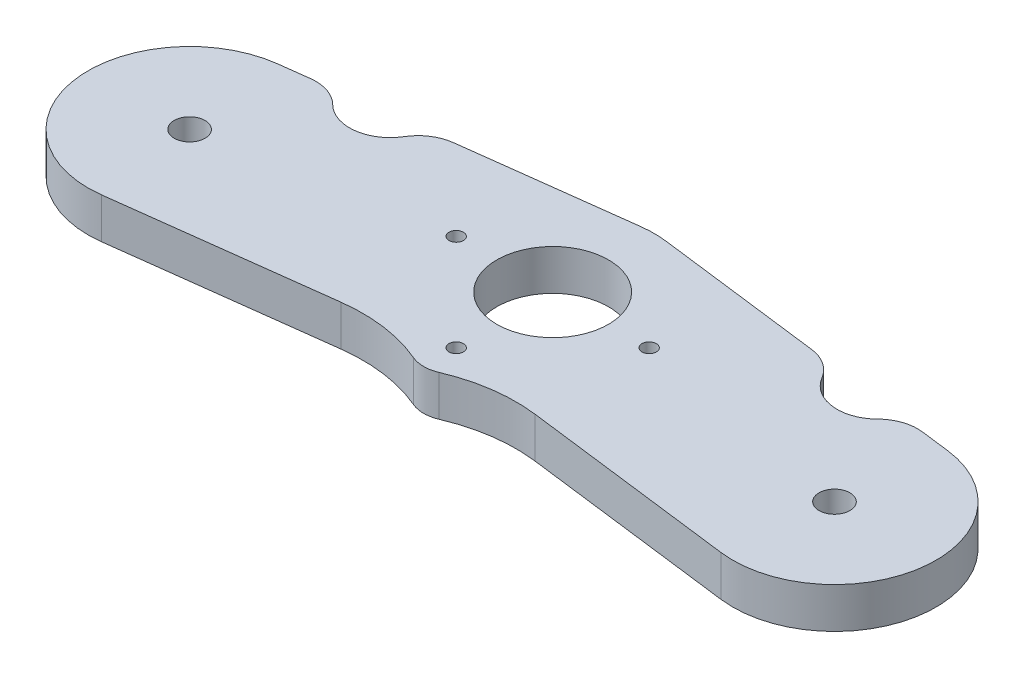
SolidWorks part; units mm, degrees
material "5052-H32"
ref_plane "Front Plane" through (0, 0, 0) normal (0, 0, 1) x (1, 0, 0)
ref_plane "Top Plane" through (0, 0, 0) normal (0, 1, 0) x (1, 0, 0)
ref_plane "Right Plane" through (0, 0, 0) normal (1, 0, 0) x (0, 0, -1)
sketch "Sketch1" plane through (0, 0, 0) normal (0, 1, 0) x (1, 0, 0)
  line L0 (50.8, 0) -> (-50.8, 0) construction
  line L1 (50.8, -15.875) -> (-50.8, -15.875) construction
  line L2 (50.8, 15.875) -> (-50.8, 15.875) construction
  line L3 (0, 0) -> (-50.4016, -6.35) construction
  line L6 (1.9844, -15.7505) -> (-48.4172, -22.1005)
  line L9 (-1.9844, 15.7505) -> (-52.3859, 9.4005)
  line L10 (0, 0) -> (50.4016, -6.35) construction
  line L11 (1.9844, 15.7505) -> (52.3859, 9.4005)
  line L12 (-1.9844, -15.7505) -> (48.4172, -22.1005)
  arc A0 (50.8, -15.875) -> (50.8, 15.875) centre (50.8, 0) ccw construction
  arc A1 (-50.8, 15.875) -> (-50.8, -15.875) centre (-50.8, 0) ccw construction
  arc A6 (1.9844, -15.7505) -> (-1.9844, 15.7505) centre (0, 0) ccw
  arc A7 (-52.3859, 9.4005) -> (-48.4172, -22.1005) centre (-50.4016, -6.35) ccw
  arc A8 (1.9844, 15.7505) -> (-1.9844, -15.7505) centre (0, 0) ccw
  arc A9 (48.4172, -22.1005) -> (52.3859, 9.4005) centre (50.4016, -6.35) ccw
  circle A10 centre (0, -15.0812) radius 5.08
  point P2 (0, 0)
  point P8 (-25.2008, -3.175)
  point P15 (25.2008, -3.175)
  point P22 (0, 0)
  dimension "D5" = 10.16
  dimension "D1" = 31.75
  dimension "D2" = 101.6
  dimension "D3" = 50.8
  dimension "D4" = 6.35
  dimension "D6" = 15.0812
extrude "Boss-Extrude1" add sketch "Sketch1" along normal blind 6.35 contours A8 L9 A7 L6 L12 | A6 A8 L12 L6 | L12 A9 L11 A6 L6 | A10 A6 A8 | L6 A10 L12 | A8 A10 L6 L12 | L12 A10 A6 L6
hole_wizard "#10-32 Tapped Hole1" positions "Sketch5" profile "Sketch6" tap size "#10-32" standard "ANSI Inch" end condition through all
sketch "Sketch5" plane through (0, 6.35, 0) normal (0, 1, 0) x (1, 0, 0)
  point P0 (-50.4016, -6.35)
  point P3 (50.4016, -6.35)
  point P32 (0, 0)
  point P33 (-50.4016, -6.35)
  point P35 (50.4016, -6.35)
sketch "Sketch6" plane through (-50.4016, 6.35, 6.35) normal (1, 0, 0) x (0, 0, 1)
  line L0 (0, 0) -> (0, 6.35)
  line L1 (0, 6.35) -> (2.413, 6.35)
  line L2 (2.413, 6.35) -> (2.413, 0)
  line L5 (2.413, 0) -> (0, 0)
  line L11 (0, -6.35) -> (0, 107.95) construction
  dimension "Thread Major Dia." = 4.826
  dimension "Thru Tap Drill Depth" = 6.35
sketch "Sketch7" plane through (0, 6.35, 0) normal (0, 1, 0) x (1, 0, 0)
  circle A0 centre (0, 0) radius 8.7312
  dimension "D1" = 17.4625
extrude "Cut-Extrude1" cut sketch "Sketch7" against normal through all
sketch "Sketch8" plane through (0, 6.35, 0) normal (0, 1, 0) x (1, 0, 0)
  line L0 (-38.1, 12.7) -> (0, 0) construction
  line L1 (0, 0) -> (38.1, 12.7) construction
  circle A0 centre (-38.1, 12.7) radius 6.35
  circle A1 centre (38.1, 12.7) radius 6.35
  point P6 (0, 0)
  dimension "D3" = 12.7
  dimension "D1" = 76.2
  dimension "D2" = 12.7
extrude "Cut-Extrude2" cut sketch "Sketch8" against normal through all
fillet "Fillet1" radius 25.4 2 edges at (-4.8443, 3.175, 16.6108) (4.8443, 3.175, 16.6108)
fillet "Fillet2" radius 6.35 4 edges at (31.7892, 3.175, -11.9954) (44.0388, 3.175, -10.4521) (-44.0388, 3.175, -10.4521) (-31.7892, 3.175, -11.9954)
hole_wizard "#4-40 Tapped Hole1" positions "Sketch9" profile "Sketch10" tap size "#4-40" standard "ANSI Inch" end condition through all
sketch "Sketch9" plane through (0, 6.35, 0) normal (0, 1, 0) x (1, 0, 0)
  circle A0 centre (0, 0) radius 15.0813 construction
  point P0 (-15.0812, 0)
  point P2 (15.0812, 0)
  point P4 (0, -15.0812)
  point P11 (-13.8113, 0)
  point P12 (0, -13.8113)
  point P13 (13.8113, 0)
  dimension "D1" = 30.1625
sketch "Sketch10" plane through (-15.0812, 6.35, 0) normal (1, 0, 0) x (0, 0, 1)
  line L0 (0, 0) -> (0, 6.35)
  line L1 (0, 6.35) -> (1.1303, 6.35)
  line L2 (1.1303, 6.35) -> (1.1303, 0)
  line L5 (1.1303, 0) -> (0, 0)
  line L11 (0, -6.35) -> (0, 107.95) construction
  dimension "Thru Tap Drill Dia." = 2.2606
  dimension "Thru Tap Drill Depth" = 6.35
cosmetic thread "Hole Thread1" parameters "D2"=2.8448
cosmetic thread "Hole Thread2" parameters "D2"=2.8448
cosmetic thread "Hole Thread3" parameters "D2"=2.8448
equation "\"D1@Sketch7\"=.5+2*0.09375"
